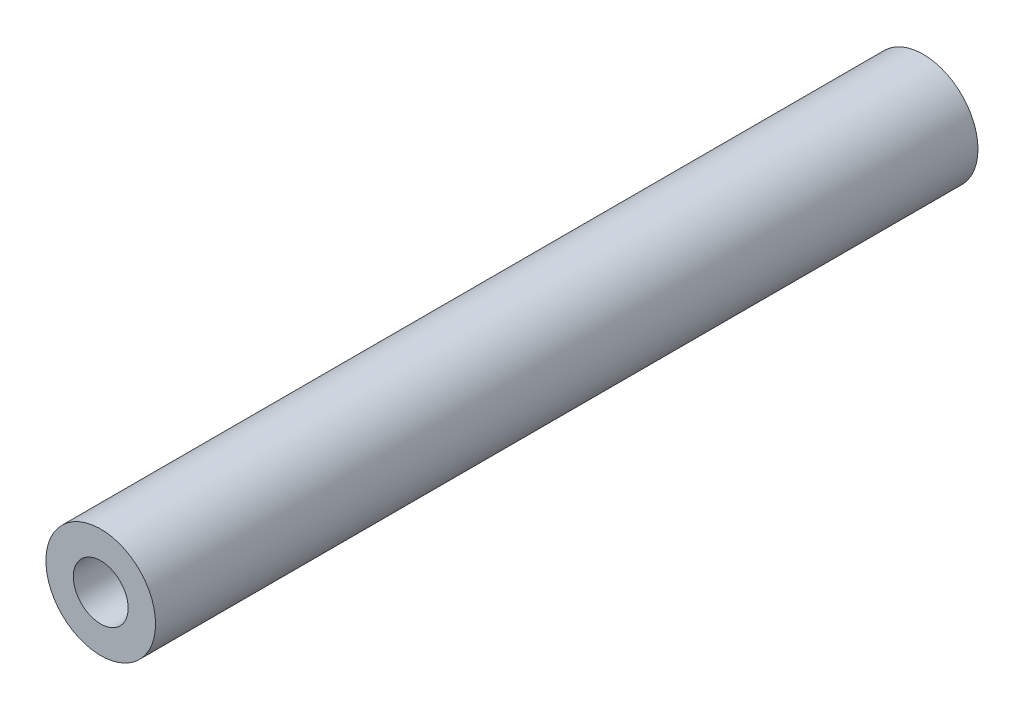
SolidWorks part; units mm, degrees
ref_plane "Front Plane" through (0, 0, 0) normal (0, 0, 1) x (1, 0, 0)
ref_plane "Top Plane" through (0, 0, 0) normal (0, 1, 0) x (1, 0, 0)
ref_plane "Right Plane" through (0, 0, 0) normal (1, 0, 0) x (0, 0, -1)
sketch "Esquisse1" plane through (0, 0, 0) normal (0, 0, 1) x (1, 0, 0)
  circle A0 centre (0, 0) radius 1.5
  circle A1 centre (0, 0) radius 3
  dimension "D1" = 6
  dimension "D2" = 3
extrude "Boss.-Extru.1" add sketch "Esquisse1" along normal blind 45
